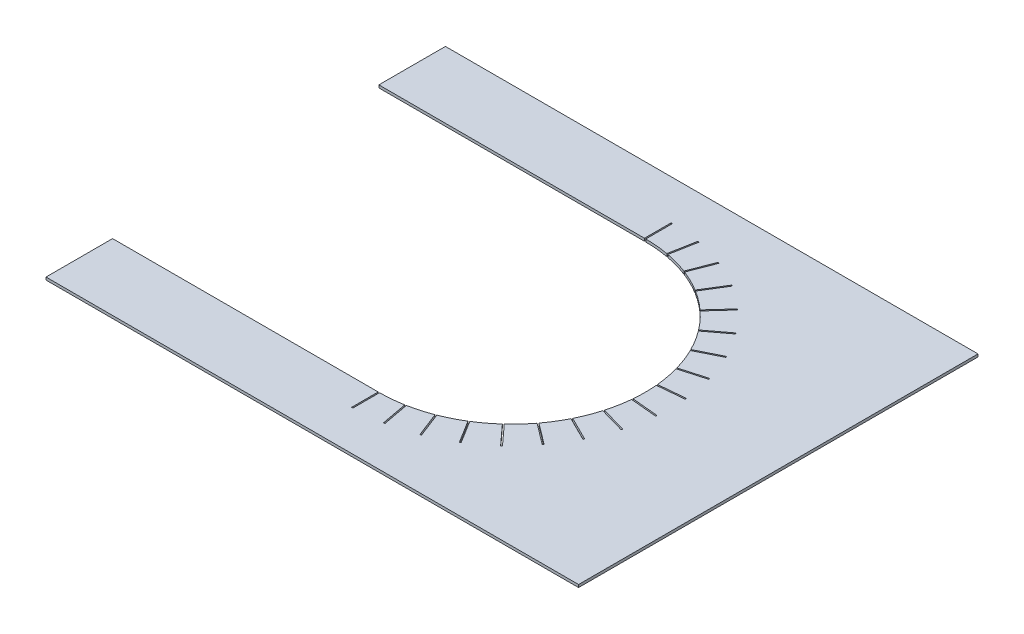
SolidWorks part; units mm, degrees
ref_plane "Vorne" through (0, 0, 0) normal (0, 0, 1) x (1, 0, 0)
ref_plane "Oben" through (0, 0, 0) normal (0, 1, 0) x (1, 0, 0)
ref_plane "Rechts" through (0, 0, 0) normal (1, 0, 0) x (0, 0, -1)
sketch "Skizze1" plane through (0, 0, 0) normal (0, 1, 0) x (1, 0, 0)
  line L0 (0, 50) -> (-100, 50)
  line L1 (-100, 50) -> (-100, 75)
  line L2 (-100, 75) -> (100, 75)
  line L3 (100, 75) -> (100, -75)
  line L4 (100, -75) -> (-100, -75)
  line L5 (-100, -75) -> (-100, -50)
  line L6 (-100, -50) -> (0, -50)
  line L7 (-50, 0) -> (50, 0) construction
  arc A0 (0, -50) -> (0, 50) centre (0, 0) ccw
  point P10 (100, 0)
  dimension "D1" = 100
  dimension "D2" = 200
  dimension "D3" = 150
  dimension "D4" = 100
extrude "Aufsatz-Linear austragen1" add sketch "Skizze1" along normal blind 1 contours L0 L1 L2 L3 L4 L5 L6 A0
sketch "Skizze2" plane through (0, 0, 0) normal (0, 1, 0) x (1, 0, 0)
  line L0 (0, 45) -> (0, 60)
  circle A0 centre (0, 0) radius 60 construction
  circle A1 centre (0, 0) radius 45 construction
  dimension "D1" = 120
  dimension "D2" = 90
extrude "Schnitt-Linear-Austragen-Dünn4" cut sketch "Skizze2" along normal blind 2 thin thin type mid plane wall 0.5
pattern_circular "Kreismuster12" count 18 over 180 about axis through (0, 0, 0) along (0, 1, 0) of "Schnitt-Linear-Austragen-Dünn4"
